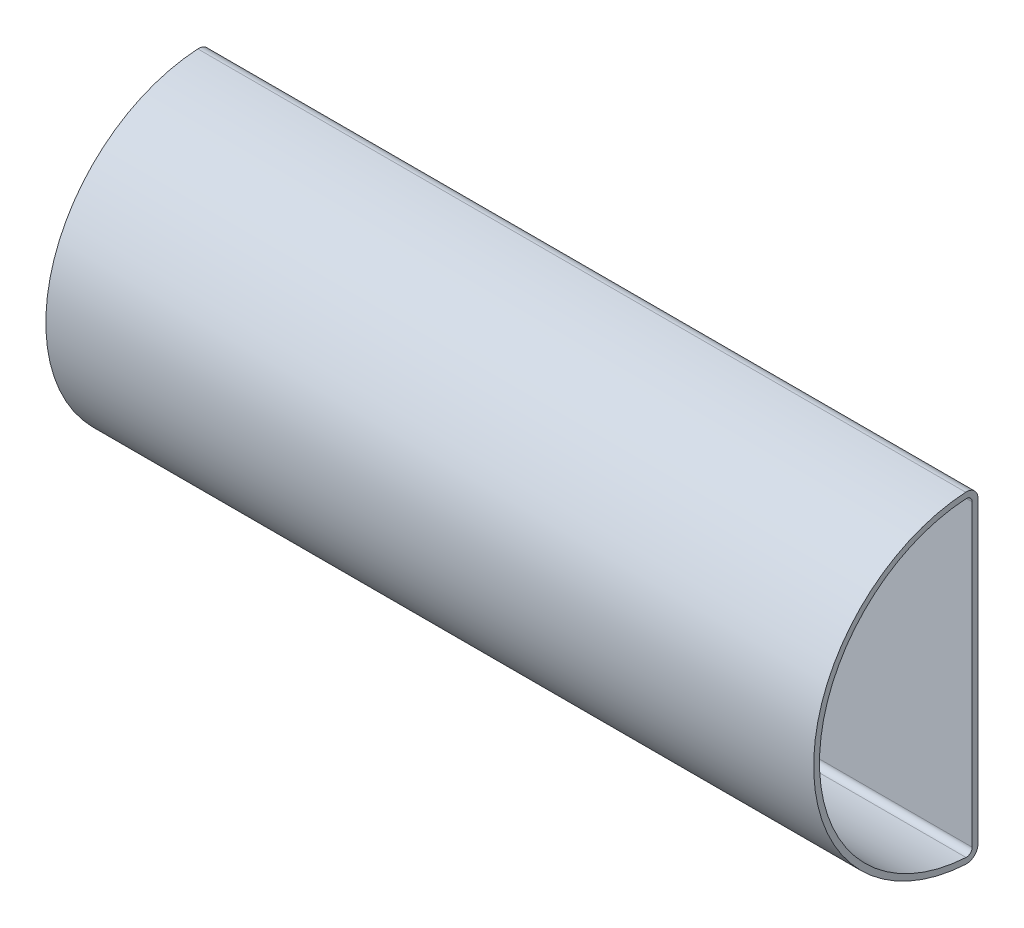
SolidWorks part; units mm, degrees
ref_plane "Front Plane" through (0, 0, 0) normal (0, 0, 1) x (1, 0, 0)
ref_plane "Top Plane" through (0, 0, 0) normal (0, 1, 0) x (1, 0, 0)
ref_plane "Right Plane" through (0, 0, 0) normal (1, 0, 0) x (0, 0, -1)
sketch "Sketch1" plane through (0, 0, 0) normal (1, 0, 0) x (0, 0, -1)
  line L0 (-8.7836, 51.4125) -> (-8.7836, -51.4125) construction
  line L1 (-7.7836, 51.4125) -> (-7.7836, -51.4125)
  line L2 (-9.7836, 51.4125) -> (-9.7836, -51.4125)
  arc A0 (-11.9583, 54.4075) -> (-11.9583, -54.4075) centre (-8.7836, 0) ccw construction
  arc A1 (-8.7836, -51.4125) -> (-11.9583, -54.4075) centre (-11.7836, -51.4125) cw construction
  arc A2 (-8.7836, 51.4125) -> (-11.9583, 54.4075) centre (-11.7836, 51.4125) ccw construction
  arc A3 (-7.7836, -51.4125) -> (-12.0166, -55.4058) centre (-11.7836, -51.4125) cw
  arc A4 (-12.0166, 55.4058) -> (-12.0166, -55.4058) centre (-8.7836, 0) ccw
  arc A5 (-7.7836, 51.4125) -> (-12.0166, 55.4058) centre (-11.7836, 51.4125) ccw
  arc A6 (-9.7836, -51.4125) -> (-11.9001, -53.4092) centre (-11.7836, -51.4125) cw
  arc A7 (-11.9001, 53.4092) -> (-11.9001, -53.4092) centre (-8.7836, 0) ccw
  arc A8 (-9.7836, 51.4125) -> (-11.9001, 53.4092) centre (-11.7836, 51.4125) ccw
  point P5 (-8.7836, -54.5)
  point P8 (-8.7836, 54.5)
  dimension "D1" = 109
  dimension "D2" = 3
  dimension "D3" = 1
  dimension "D4" = 1
extrude "Boss-Extrude1" add sketch "Sketch1" along normal blind 264
